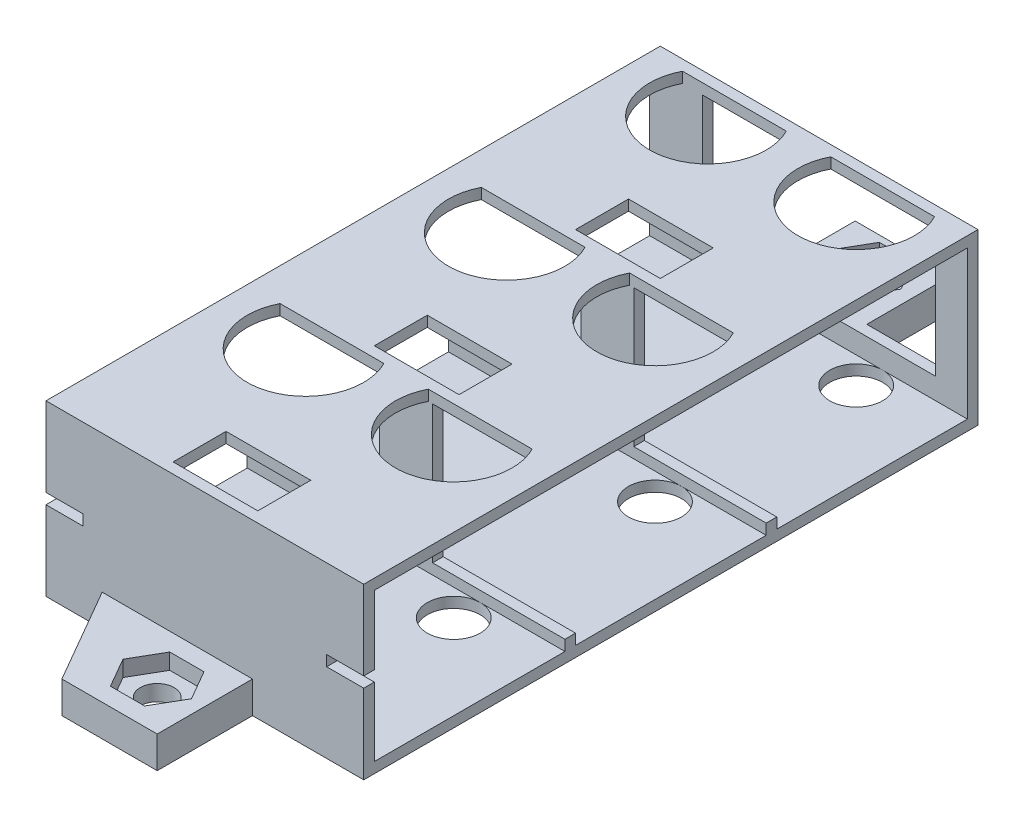
SolidWorks part; units mm, degrees
ref_plane "Front Plane" through (0, 0, 0) normal (0, 0, 1) x (1, 0, 0)
ref_plane "Top Plane" through (0, 0, 0) normal (0, 1, 0) x (1, 0, 0)
ref_plane "Right Plane" through (0, 0, 0) normal (1, 0, 0) x (0, 0, -1)
sketch "Sketch3" plane through (0, 0, 0) normal (1, 0, 0) x (0, 0, -1)
  line L0 (1, 1) -> (19, 1)
  line L1 (0, 0) -> (58, 0)
  line L2 (0, 0) -> (0, 16)
  line L3 (0, 16) -> (58, 16)
  line L4 (58, 0) -> (58, 16)
  line L5 (57, 1) -> (57, 15)
  line L6 (1, 15) -> (57, 15)
  line L7 (1, 1) -> (1, 15)
  line L8 (20, 2) -> (38, 2) construction
  line L9 (20, 1) -> (38, 1)
  line L10 (38, 1) -> (38, 2)
  line L11 (38, 2) -> (39, 2)
  line L12 (39, 1) -> (39, 2)
  line L14 (19, 1) -> (19, 2)
  line L15 (19, 2) -> (20, 2)
  line L16 (20, 1) -> (20, 2)
  line L17 (39, 1) -> (57, 1)
  line L19 (1, 1) -> (57, 1) construction
  point P17 (20, 1.5)
extrude "Boss-Extrude2" add sketch "Sketch3" along normal blind 30
sketch "Sketch4" plane through (0, 1, 0) normal (0, 1, 0) x (1, 0, 0)
  line L0 (8, 1) -> (8, 57) construction
  line L1 (30, 1) -> (0, 1) construction
  line L2 (30, 57) -> (0, 57) construction
  line L3 (22, 1) -> (22, 57) construction
  line L4 (0, 39) -> (0, 57) construction
  line L5 (30, 39) -> (30, 57) construction
  line L6 (8, 54.5) -> (22, 54.5) construction
  line L7 (8, 35.5) -> (22, 35.5) construction
  line L8 (8, 16.5) -> (22, 16.5) construction
  line L9 (30, 38) -> (0, 38) construction
  line L10 (30, 19) -> (0, 19) construction
  circle A0 centre (22, 54.5) radius 2.5
  circle A1 centre (8, 54.5) radius 2.5
  circle A2 centre (8, 35.5) radius 2.5
  circle A3 centre (22, 35.5) radius 2.5
  circle A4 centre (8, 16.5) radius 2.5
  circle A5 centre (22, 16.5) radius 2.5
extrude "Cut-Extrude2" cut sketch "Sketch4" against normal up to next
sketch "Sketch7" plane through (0, 0, -57) normal (0, 0, 1) x (1, 0, 0)
  line L0 (30, 1) -> (30, 15) construction
  line L1 (5, 15) -> (27, 15)
  line L2 (5, 15) -> (5, 3)
  line L3 (5, 3) -> (27, 3)
  line L4 (27, 15) -> (27, 3)
  line L5 (30, 15) -> (0, 15) construction
  line L6 (26, 3) -> (26, 1) construction
  line L7 (0, 1) -> (0, 15) construction
  line L8 (30, 1) -> (22, 1) construction
  dimension "D1" = 3
  dimension "D2" = 2
  dimension "D3" = 5
extrude "Cut-Extrude6" cut sketch "Sketch7" against normal up to next
sketch "Sketch9" plane through (0, 2, 0) normal (0, 1, 0) x (1, 0, 0)
  line L0 (30, 19) -> (0, 19) construction
  line L1 (12.5, 19) -> (17.5, 19)
  line L2 (12.5, 19) -> (12.5, 20)
  line L3 (12.5, 20) -> (17.5, 20)
  line L4 (17.5, 19) -> (17.5, 20)
  line L5 (30, 20) -> (0, 20) construction
  line L6 (15, 19) -> (15, 20) construction
  line L7 (30, 38) -> (0, 38) construction
  line L8 (12.5, 38) -> (17.5, 38)
  line L9 (12.5, 38) -> (12.5, 39)
  line L10 (12.5, 39) -> (17.5, 39)
  line L11 (17.5, 38) -> (17.5, 39)
  line L12 (30, 39) -> (0, 39) construction
  line L13 (12.5, 20) -> (12.5, 38) construction
  line L14 (17.5, 38) -> (17.5, 20) construction
  dimension "D1" = 5
extrude "Boss-Extrude4" add sketch "Sketch9" along normal up to next
chamfer "Chamfer1" distance 5 angle 45 2 edges at (12.5, 2, -19.5) (12.5, 2, -38.5)
sketch "Sketch10" plane through (0, 0, 0) normal (0, -1, 0) x (1, 0, 0)
  line L0 (30, 0) -> (0, 0) construction
  line L1 (19.5, 0) -> (5.3038, 0)
  line L2 (19.5, 0) -> (19.5, 9)
  line L3 (19.5, 9) -> (10.5, 9)
  line L4 (5.3038, 0) -> (10.5, 9)
  line L5 (15, 9) -> (15, 0) construction
  line L6 (30, 0) -> (30, -58) construction
  line L7 (30, -58) -> (0, -58) construction
  line L8 (19.5, -58) -> (10.5, -58)
  line L9 (19.5, -58) -> (19.5, -67)
  line L10 (19.5, -67) -> (10.5, -67)
  line L11 (10.5, -67) -> (5.3038, -58) construction
  line L12 (19.5, 0) -> (19.5, -58) construction
  line L13 (15, 0) -> (15, -67) construction
  line L14 (15, -62.5) -> (19.5, -62.5) construction
  line L15 (10.5, -67) -> (10.5, -58)
  line L16 (30, 0) -> (0, 0) construction
  line L17 (5.3038, -58) -> (5.3038, 0) construction
  line L20 (10.5, -65.9) -> (10.5, -54) construction
  line L21 (30, -58) -> (0, -58) construction
  circle A0 centre (15, 4.5) radius 1.6
  circle A1 centre (15, -62.5) radius 1.6
extrude "Boss-Extrude5" add sketch "Sketch10" against normal blind 3
sketch "Sketch11" plane through (0, 3, 0) normal (0, 1, 0) x (1, 0, 0)
  line L1 (11.7668, 62.5) -> (13.3834, 59.7)
  line L2 (13.3834, 59.7) -> (16.6166, 59.7)
  line L3 (16.6166, 59.7) -> (18.2332, 62.5)
  line L4 (18.2332, 62.5) -> (16.6166, 65.3)
  line L5 (16.6166, 65.3) -> (13.3834, 65.3)
  line L6 (13.3834, 65.3) -> (11.7668, 62.5)
  line L7 (11.7668, -4.5) -> (13.3834, -7.3)
  line L8 (13.3834, -7.3) -> (16.6166, -7.3)
  line L9 (16.6166, -7.3) -> (18.2332, -4.5)
  line L10 (18.2332, -4.5) -> (16.6166, -1.7)
  line L11 (16.6166, -1.7) -> (13.3834, -1.7)
  line L12 (13.3834, -1.7) -> (11.7668, -4.5)
  circle A0 centre (15, 62.5) radius 2.8 construction
  circle A1 centre (15, -4.5) radius 2.8 construction
  dimension "D1" = 5.6
  dimension "D2" = 5.6
extrude "Cut-Extrude8" cut sketch "Sketch11" against normal blind 1.5
sketch "Sketch12" plane through (0, 0, 0) normal (0, 0, 1) x (1, 0, 0)
  line L0 (0, 8) -> (30, 8) construction
  line L1 (0, 16) -> (0, 0) construction
  line L2 (30, 16) -> (30, 0) construction
  line L4 (0, 8.5) -> (3.5, 8.5)
  line L5 (0, 8.5) -> (0, 7.5)
  line L6 (0, 7.5) -> (3.5, 7.5)
  line L7 (3.5, 8.5) -> (3.5, 7.5)
  line L8 (30, 8.5) -> (26.5, 8.5)
  line L9 (30, 8.5) -> (30, 7.5)
  line L10 (30, 7.5) -> (26.5, 7.5)
  line L11 (26.5, 8.5) -> (26.5, 7.5)
  point P14 (0, 8)
  point P17 (0, 8)
  point P18 (30, 8)
extrude "Cut-Extrude9" cut sketch "Sketch12" against normal up to next
sketch "Sketch13" plane through (0, 0, 0) normal (0, -1, 0) x (1, 0, 0)
  line L0 (19.5, -58) -> (19.5, -67) construction
  line L1 (10.5, -67) -> (19.5, -67)
  line L2 (10.5, -67) -> (10.5, -65.9)
  line L3 (10.5, -65.9) -> (19.5, -65.9)
  line L4 (19.5, -67) -> (19.5, -65.9)
  dimension "D1" = 1.1
extrude "Cut-Extrude10" cut sketch "Sketch13" against normal up to next
sketch "Sketch14" plane through (0, 16, 0) normal (0, 1, 0) x (1, 0, 0)
  line L0 (11, 6) -> (11, 20) construction
  line L1 (12.899, 57) -> (3.101, 57)
  line L2 (5, 57) -> (0, 57)
  line L3 (26.899, 57) -> (17.101, 57)
  line L4 (11, 25) -> (11, 39) construction
  line L6 (17.5, 38) -> (12.5, 38)
  line L7 (26.899, 38) -> (17.101, 38)
  line L8 (12.899, 38) -> (3.101, 38)
  line L9 (17.5, 19) -> (12.5, 19)
  line L10 (26.899, 19) -> (17.101, 19)
  line L11 (12.899, 19) -> (3.101, 19)
  line L12 (15, 1) -> (15, 0) construction
  line L13 (19, 44) -> (11, 44)
  line L14 (19, 44) -> (19, 39)
  line L15 (19, 39) -> (11, 39)
  line L16 (11, 44) -> (11, 39)
  line L17 (19, 25) -> (11, 25)
  line L18 (19, 25) -> (19, 20)
  line L19 (19, 20) -> (11, 20)
  line L20 (11, 25) -> (11, 20)
  line L21 (19, 6) -> (11, 6)
  line L22 (19, 6) -> (19, 1)
  line L23 (19, 1) -> (11, 1)
  line L24 (11, 6) -> (11, 1)
  line L25 (30, 0) -> (0, 0) construction
  line L26 (19, 6) -> (19, 20) construction
  line L27 (19, 25) -> (19, 39) construction
  line L28 (12.5, 39) -> (17.5, 39) construction
  line L29 (12.5, 20) -> (17.5, 20) construction
  line L30 (30, 1) -> (0, 1) construction
  circle A2 centre (8, 54.5) radius 5.5
  arc A3 (3.101, 57) -> (12.899, 57) centre (8, 54.5) ccw
  circle A5 centre (22, 54.5) radius 5.5
  arc A6 (17.101, 57) -> (26.899, 57) centre (22, 54.5) ccw
  circle A8 centre (8, 35.5) radius 5.5
  arc A9 (3.101, 38) -> (12.899, 38) centre (8, 35.5) ccw
  circle A11 centre (22, 35.5) radius 5.5
  arc A12 (17.101, 38) -> (26.899, 38) centre (22, 35.5) ccw
  circle A14 centre (8, 16.5) radius 5.5
  arc A15 (3.101, 19) -> (12.899, 19) centre (8, 16.5) ccw
  circle A17 centre (22, 16.5) radius 5.5
  arc A18 (17.101, 19) -> (26.899, 19) centre (22, 16.5) ccw
extrude "Cut-Extrude12" cut sketch "Sketch14" against normal up to next
equation "\"D8@Sketch3\"=\"D7@Sketch3\""
equation "\"D7@Sketch3\"=(\"D3@Sketch3\"-\"D5@Sketch3\"*2)/3"
equation "\"D6@Sketch3\"=\"D5@Sketch3\""
equation "\"D2@Sketch4\"=\"D1@Sketch4\""
equation "\"D4@Sketch4\"=\"D3@Sketch4\""
equation "\"D5@Sketch4\"=\"D3@Sketch4\""
equation "\"D7@Sketch4\"=\"D6@Sketch4\""
equation "\"D8@Sketch4\"=\"D6@Sketch4\""
equation "\"D9@Sketch4\"=\"D6@Sketch4\""
equation "\"D10@Sketch4\"=\"D6@Sketch4\""
equation "\"D11@Sketch4\"=\"D6@Sketch4\""
equation "\"D4@Sketch10\"=\"D3@Sketch10\""
equation "\"D6@Sketch10\"=\"D5@Sketch10\""
equation "\"D2@Sketch12\"=\"D1@Sketch12\""
equation "\"D4@Sketch12\"=\"D3@Sketch12\""
equation "\"D12@Sketch14\"=\"D11@Sketch14\""
equation "\"D13@Sketch14\"=\"D11@Sketch14\""
